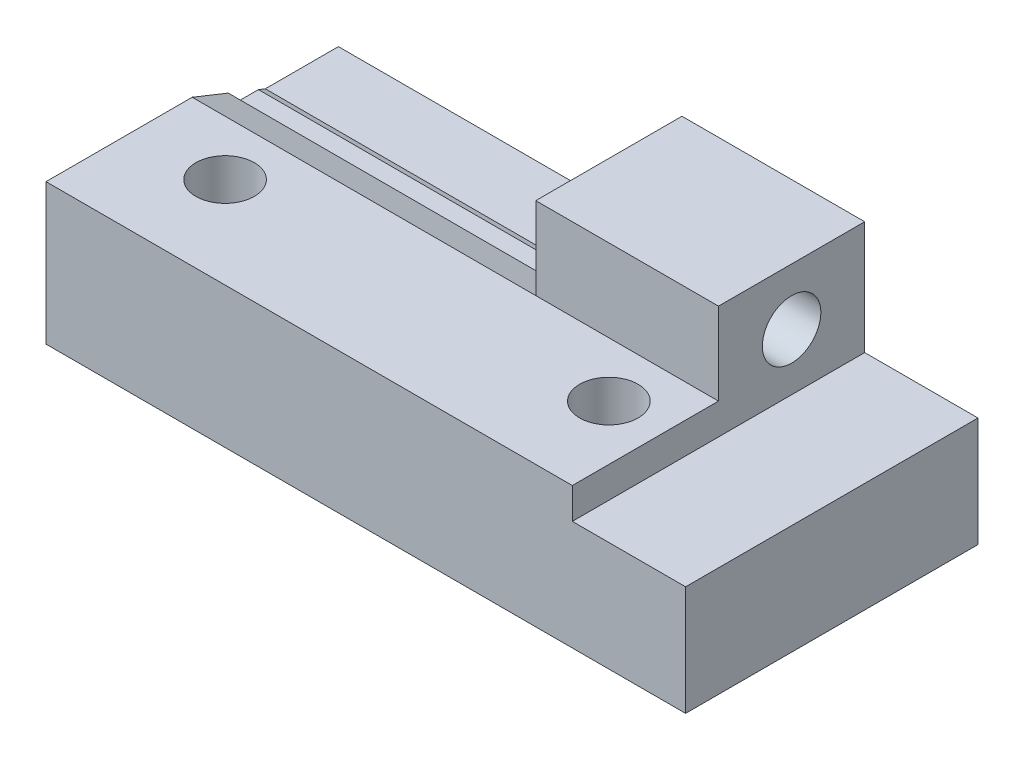
SolidWorks part; units mm, degrees
ref_plane "Alzado" through (0, 0, 0) normal (0, 0, 1) x (1, 0, 0)
ref_plane "Planta" through (0, 0, 0) normal (0, 1, 0) x (1, 0, 0)
ref_plane "Vista lateral" through (0, 0, 0) normal (1, 0, 0) x (0, 0, -1)
sketch "Croquis1" plane through (0, 0, 0) normal (0, 0, 1) x (1, 0, 0)
  line L0 (0, 0) -> (0, 6)
  line L1 (0, 6) -> (-6.2, 6)
  line L2 (-6.2, 6) -> (-6.2, 12.2)
  line L3 (-6.2, 12.2) -> (-35, 12.2)
  line L4 (-35, 12.2) -> (-35, 0)
  line L5 (-35, 0) -> (0, 0)
  dimension "D1" = 6
  dimension "D2" = 6.2
  dimension "D3" = 6.2
  dimension "D4" = 35
extrude "Saliente-Extruir1" add sketch "Croquis1" along normal blind 8
sketch "Croquis2" plane through (0, 0, 8) normal (0, 0, 1) x (1, 0, 0)
  line L0 (-6.2, 7.7) -> (-35, 7.7)
  line L1 (-6.2, 12.2) -> (-35, 12.2) construction
  line L6 (-35, 0) -> (0, 0)
  line L7 (0, 0) -> (0, 6)
  line L8 (0, 6) -> (-6.2, 6)
  line L9 (-6.2, 6) -> (-6.2, 12.2)
  line L10 (-6.2, 12.2) -> (-35, 12.2)
  line L11 (-35, 12.2) -> (-35, 0)
  line L12 (-35, 0) -> (0, 0)
  line L13 (0, 0) -> (0, 6)
  line L14 (0, 6) -> (-6.2, 6)
  line L15 (-6.2, 6) -> (-6.2, 7.7)
  line L17 (-35, 7.7) -> (-35, 0)
  dimension "D2" = 4.5
  dimension "D1" = 0
extrude "Saliente-Extruir2" add sketch "Croquis2" along normal blind 8
sketch "Croquis3" plane through (-6.2, 0, 0) normal (1, 0, 0) x (0, 0, -1)
  line L0 (-16, 6) -> (0, 6) construction
  line L1 (0, 6) -> (0, 12.2) construction
  circle A0 centre (-4, 9.1) radius 1.6
  dimension "D3" = 3.2
  dimension "D1" = 3.1
  dimension "D2" = 4
extrude "Cortar-Extruir1" cut sketch "Croquis3" against normal up to next
sketch "Croquis4" plane through (0, 7.7, 0) normal (0, 1, 0) x (1, 0, 0)
  line L0 (-30.2, -11) -> (-9.2, -11) construction
  line L1 (-9.2, -11) -> (-6.2, -11) construction
  line L2 (-6.2, -16) -> (-6.2, -8) construction
  line L3 (-9.2, -11) -> (-9.2, -8) construction
  line L4 (-6.2, -8) -> (-35, -8) construction
  circle A0 centre (-30.2, -11) radius 1.6
  circle A1 centre (-9.2, -11) radius 1.6
  dimension "D4" = 3.2
  dimension "D1" = 21
  dimension "D2" = 3
  dimension "D3" = 3
extrude "Cortar-Extruir2" cut sketch "Croquis4" against normal up to next
sketch "Croquis5" plane through (0, 0, 0) normal (0, -1, 0) x (1, 0, 0)
  line L1 (-33.4909, 11) -> (-31.8454, 8.15)
  line L2 (-31.8454, 8.15) -> (-28.5546, 8.15)
  line L3 (-28.5546, 8.15) -> (-26.9091, 11)
  line L4 (-26.9091, 11) -> (-28.5546, 13.85)
  line L5 (-28.5546, 13.85) -> (-31.8454, 13.85)
  line L6 (-31.8454, 13.85) -> (-33.4909, 11)
  line L7 (-12.4909, 11) -> (-10.8454, 8.15)
  line L8 (-10.8454, 8.15) -> (-7.5546, 8.15)
  line L9 (-7.5546, 8.15) -> (-5.9091, 11)
  line L10 (-5.9091, 11) -> (-7.5546, 13.85)
  line L11 (-7.5546, 13.85) -> (-10.8454, 13.85)
  line L12 (-10.8454, 13.85) -> (-12.4909, 11)
  circle A0 centre (-30.2, 11) radius 2.85 construction
  circle A1 centre (-9.2, 11) radius 2.85 construction
  dimension "D1" = 5.7
extrude "Cortar-Extruir3" cut sketch "Croquis5" against normal blind 3
sketch "Croquis6" plane through (-35, 0, 0) normal (-1, 0, 0) x (0, 0, 1)
  line L0 (8, 7.7) -> (4, 6.1)
  line L1 (4, 6.1) -> (0, 6.1)
  line L6 (0, 12.2) -> (0, 0)
  line L7 (0, 0) -> (16, 0)
  line L8 (16, 0) -> (16, 7.7)
  line L9 (16, 7.7) -> (8, 7.7)
  line L10 (8, 7.7) -> (8, 12.2)
  line L11 (8, 12.2) -> (0, 12.2)
  line L12 (0, 12.2) -> (0, 6.1)
  line L16 (8, 7.7) -> (8, 12.2)
  line L17 (8, 12.2) -> (0, 12.2)
  dimension "D2" = 4
  dimension "D3" = 6.1
  dimension "D1" = 0
extrude "Cortar-Extruir4" cut sketch "Croquis6" against normal offset from surface (18.8 mm away) 10 up to face at (-6.2, 10.7, 4)
sketch "Croquis7" plane through (-16.2, 0, 0) normal (-1, 0, 0) x (0, 0, 1)
  line L1 (0.7091, 9.1) -> (2.3546, 6.25)
  line L2 (2.3546, 6.25) -> (5.6454, 6.25)
  line L3 (5.6454, 6.25) -> (7.2909, 9.1)
  line L4 (7.2909, 9.1) -> (5.6454, 11.95)
  line L5 (5.6454, 11.95) -> (2.3546, 11.95)
  line L6 (2.3546, 11.95) -> (0.7091, 9.1)
  circle A0 centre (4, 9.1) radius 2.85 construction
  dimension "D1" = 5.7
extrude "Cortar-Extruir5" cut sketch "Croquis7" against normal blind 3 and the other way up to next
